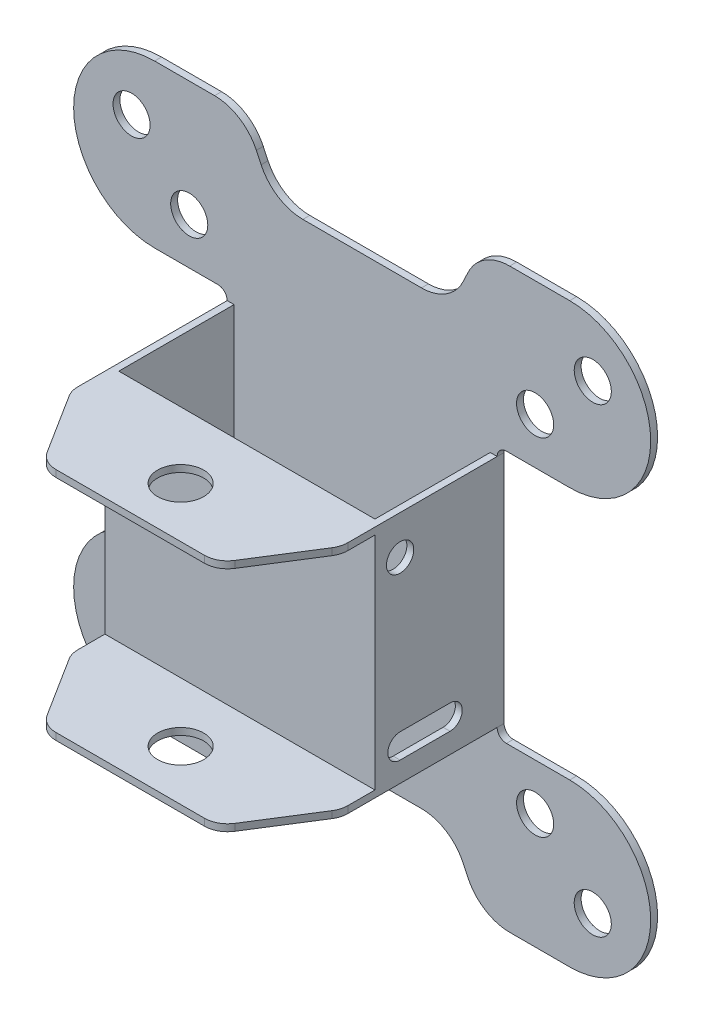
SolidWorks part; units mm, degrees
material "Plain Carbon Steel"
ref_plane "Front Plane" through (0, 0, 0) normal (0, 0, 1) x (1, 0, 0)
ref_plane "Top Plane" through (0, 0, 0) normal (0, 1, 0) x (1, 0, 0)
ref_plane "Right Plane" through (0, 0, 0) normal (1, 0, 0) x (0, 0, -1)
sketch "Sketch1" plane through (0, 0, 0) normal (0, 0, 1) x (1, 0, 0)
  line L0 (-31.2733, 27.4383) -> (-45, 27.4383)
  line L2 (29.2733, -25.4383) -> (29.2733, 25.4383)
  line L4 (-29.2733, -25.4383) -> (-29.2733, 25.4383)
  line L5 (29.2733, -27.4383) -> (-29.2733, 27.4383) construction
  line L6 (29.2733, 27.4383) -> (-29.2733, -27.4383) construction
  line L7 (-45, 27.4383) -> (-45, 62.5617) construction
  line L8 (-45, 62.5617) -> (-31.9905, 62.5617)
  line L9 (-22.9433, 56.8217) -> (-21.9125, 54.6327)
  line L10 (-12.8653, 48.8926) -> (12.8653, 48.8926)
  line L11 (0, -27.9784) -> (0, 27.9784) construction
  line L12 (-29.2733, 0) -> (29.2733, 0) construction
  line L13 (22.9433, 56.8217) -> (21.9125, 54.6327)
  line L14 (45, 62.5617) -> (31.9905, 62.5617)
  line L15 (45, 27.4383) -> (45, 62.5617) construction
  line L16 (31.2733, 27.4383) -> (45, 27.4383)
  line L17 (-45, -62.5617) -> (-31.9905, -62.5617)
  line L18 (-31.2733, -27.4383) -> (-45, -27.4383)
  line L19 (31.2733, -27.4383) -> (45, -27.4383)
  line L20 (45, -27.4383) -> (45, -62.5617) construction
  line L21 (45, -62.5617) -> (31.9905, -62.5617)
  line L22 (22.9433, -56.8217) -> (21.9125, -54.6327)
  line L23 (-22.9433, -56.8217) -> (-21.9125, -54.6327)
  line L24 (-12.8653, -48.8926) -> (12.8653, -48.8926)
  line L25 (-45, -27.4383) -> (-45, -62.5617) construction
  arc A0 (-45, 27.4383) -> (-45, 62.5617) centre (-45, 45) cw
  arc A1 (45, 27.4383) -> (45, 62.5617) centre (45, 45) ccw
  arc A2 (-45, -27.4383) -> (-45, -62.5617) centre (-45, -45) ccw
  arc A3 (45, -27.4383) -> (45, -62.5617) centre (45, -45) cw
  circle A4 centre (-50, 50) radius 4.0229
  circle A11 centre (50, 50) radius 4.0229
  arc A12 (21.9125, 54.6327) -> (12.8653, 48.8926) centre (12.8653, 58.8926) cw
  arc A13 (-21.9125, 54.6327) -> (-12.8653, 48.8926) centre (-12.8653, 58.8926) ccw
  arc A14 (-21.9125, -54.6327) -> (-12.8653, -48.8926) centre (-12.8653, -58.8926) cw
  arc A15 (21.9125, -54.6327) -> (12.8653, -48.8926) centre (12.8653, -58.8926) ccw
  arc A16 (-31.9905, -62.5617) -> (-22.9433, -56.8217) centre (-31.9905, -52.5617) ccw
  arc A17 (31.9905, -62.5617) -> (22.9433, -56.8217) centre (31.9905, -52.5617) cw
  arc A18 (22.9433, 56.8217) -> (31.9905, 62.5617) centre (31.9905, 52.5617) cw
  arc A19 (-31.9905, 62.5617) -> (-22.9433, 56.8217) centre (-31.9905, 52.5617) cw
  arc A20 (31.2733, -27.4383) -> (29.2733, -25.4383) centre (31.2733, -25.4383) cw
  arc A21 (-31.2733, -27.4383) -> (-29.2733, -25.4383) centre (-31.2733, -25.4383) ccw
  arc A22 (-31.2733, 27.4383) -> (-29.2733, 25.4383) centre (-31.2733, 25.4383) cw
  arc A23 (29.2733, 25.4383) -> (31.2733, 27.4383) centre (31.2733, 25.4383) cw
  circle A24 centre (-37.5, 37.5) radius 4.0229
  circle A25 centre (37.5, 37.5) radius 4.0229
  circle A26 centre (50, -50) radius 4.0229
  circle A27 centre (37.5, -37.5) radius 4.0229
  circle A28 centre (-37.5, -37.5) radius 4.0229
  circle A29 centre (-50, -50) radius 4.0229
  point P0 (0, 0)
  point P18 (0, 48.8926)
  point P22 (-22.4279, 55.7272)
  point P33 (-22.4279, -55.7272)
  point P53 (19.2098, 48.8926)
  point P56 (-19.2098, 48.8926)
  point P59 (-19.2098, -48.8926)
  point P62 (19.2098, -48.8926)
  point P65 (-25.646, -62.5617)
  point P68 (25.646, -62.5617)
  point P71 (25.646, 62.5617)
  point P74 (-25.646, 62.5617)
  dimension "D6" = 10
  dimension "D7" = 2
  dimension "D2" = 90
  dimension "D3" = 90
  dimension "D4" = 75
  dimension "D5" = 75
  dimension "D1" = 100
  dimension "D8" = 100
extrude "Boss-Extrude1" add sketch "Sketch1" along normal blind 1.5
sketch "Sketch3" plane through (0, 0, 1.5) normal (0, 0, 1) x (1, 0, 0)
  line L0 (-29.2733, 25.4383) -> (-29.2733, -25.4383)
  line L1 (-29.2733, -25.4383) -> (-27.7733, -25.4383)
  line L2 (-27.7733, -25.4383) -> (-27.7733, 25.4383)
  line L3 (-27.7733, 25.4383) -> (-29.2733, 25.4383)
  line L4 (0, 0) -> (0, 30.3233) construction
  line L5 (29.2733, -25.4383) -> (27.7733, -25.4383)
  line L6 (27.7733, -25.4383) -> (27.7733, 25.4383)
  line L7 (29.2733, 25.4383) -> (29.2733, -25.4383)
  line L8 (27.7733, 25.4383) -> (29.2733, 25.4383)
  dimension "D1" = 1.5
extrude "Boss-Extrude2" add sketch "Sketch3" along normal blind 25
sketch "Sketch4" plane through (0, 0, 26.5) normal (0, 0, 1) x (1, 0, 0)
  line L1 (29.2733, 25.4383) -> (-29.2733, 25.4383)
  line L2 (29.2733, 25.4383) -> (29.2733, -25.4383)
  line L3 (29.2733, -25.4383) -> (-29.2733, -25.4383)
  line L4 (-29.2733, 25.4383) -> (-29.2733, -25.4383)
extrude "Boss-Extrude3" add sketch "Sketch4" along normal blind 1.5
sketch "Sketch5" plane through (0, 25.4383, 0) normal (0, 1, 0) x (1, 0, 0)
  line L0 (-29.2733, -28) -> (-29.2733, -35.308)
  line L1 (-29.2733, -35.308) -> (-18.8716, -51.7858)
  line L2 (-18.8716, -51.7858) -> (18.8716, -51.7858)
  line L3 (0, 0) -> (0, -51.7858) construction
  line L4 (-29.2733, -28) -> (29.2733, -28)
  line L5 (29.2733, -28) -> (-29.2733, -28) construction
  line L6 (29.2733, -35.308) -> (18.8716, -51.7858)
  line L7 (29.2733, -28) -> (29.2733, -35.308)
  circle A0 centre (0, -40.8613) radius 5
  point P13 (0, -28)
  point P15 (-29.2733, -33.6693)
  point P16 (0, -44.958)
  point P17 (0, -56.1556)
  point P18 (-29.2733, -32.6679)
  point P19 (0, -40.8613)
  point P20 (0, -51.7858)
  point P21 (-29.2733, -35.308)
  dimension "D1" = 10
extrude "Boss-Extrude4" add sketch "Sketch5" against normal blind 1.5
mirror "Mirror1" about plane through (0, 0, 0) normal (0, 1, 0) of "Boss-Extrude4"
sketch "Sketch8" plane through (-29.2733, 0, 0) normal (-1, 0, 0) x (0, 0, 1)
  line L0 (11.7278, -18.3904) -> (22.5468, -18.3904) construction
  line L1 (11.7278, -15.7331) -> (22.5468, -15.7331)
  line L2 (11.7278, -21.0477) -> (22.5468, -21.0477)
  arc A0 (11.7278, -15.7331) -> (11.7278, -21.0477) centre (11.7278, -18.3904) ccw
  arc A1 (22.5468, -21.0477) -> (22.5468, -15.7331) centre (22.5468, -18.3904) ccw
  circle A2 centre (22.5468, 17.0087) radius 2.961
  point P2 (17.1373, -18.3904)
extrude "Cut-Extrude1" cut sketch "Sketch8" against normal through all
fillet "Fillet1" radius 5 8 edges at (-29.2733, 24.6883, 35.308) (-18.8716, 24.6883, 51.7858) (18.8716, 24.6883, 51.7858) (29.2733, 24.6883, 35.308) (29.2733, -24.6883, 35.308) (18.8716, -24.6883, 51.7858) (-18.8716, -24.6883, 51.7858) (-29.2733, -24.6883, 35.308)
